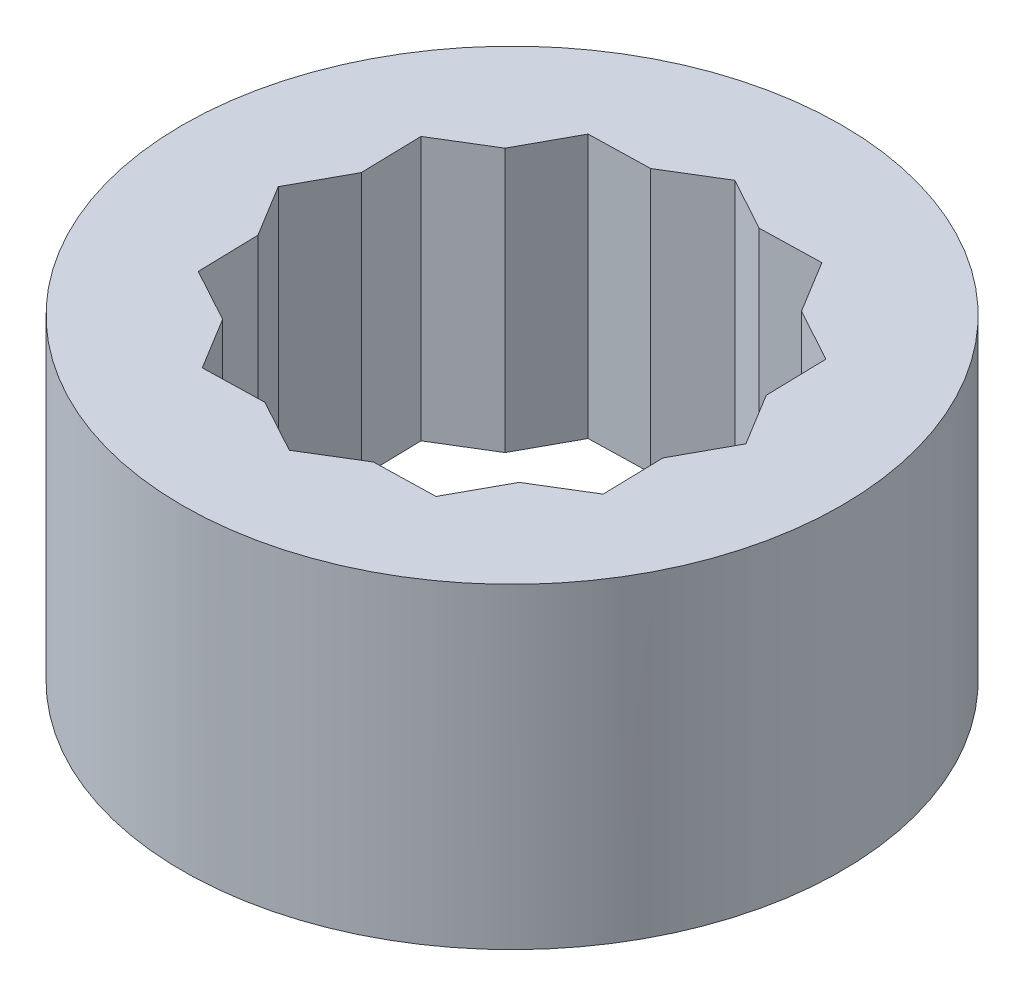
SolidWorks part; units mm, degrees
ref_plane "Front Plane" through (0, 0, 0) normal (0, 0, 1) x (1, 0, 0)
ref_plane "Top Plane" through (0, 0, 0) normal (0, 1, 0) x (1, 0, 0)
ref_plane "Right Plane" through (0, 0, 0) normal (1, 0, 0) x (0, 0, -1)
sketch "Sketch1" plane through (0, 0, 0) normal (0, 1, 0) x (1, 0, 0)
  circle A0 centre (0, 0) radius 15.875
  dimension "D1" = 31.75
extrude "Boss-Extrude1" add sketch "Sketch1" along normal blind 12.7 contours A0
sketch "Sketch2" plane through (0, 12.7, 0) normal (0, 1, 0) x (1, 0, 0)
  line L1 (9.6552, -5.2673) -> (9.3892, 5.728)
  line L2 (9.3892, 5.728) -> (-0.266, 10.9953)
  line L3 (-0.266, 10.9953) -> (-9.6552, 5.2673)
  line L4 (-9.6552, 5.2673) -> (-9.3892, -5.728)
  line L5 (-9.3892, -5.728) -> (0.266, -10.9953)
  line L6 (0.266, -10.9953) -> (9.6552, -5.2673)
  line L7 (5.728, -9.3892) -> (10.9953, 0.266)
  line L8 (10.9953, 0.266) -> (5.2673, 9.6552)
  line L9 (5.2673, 9.6552) -> (-5.728, 9.3892)
  line L10 (-5.728, 9.3892) -> (-10.9953, -0.266)
  line L11 (-10.9953, -0.266) -> (-5.2673, -9.6552)
  line L12 (-5.2673, -9.6552) -> (5.728, -9.3892)
  circle A0 centre (0, 0) radius 9.525 construction
  circle A1 centre (0, 0) radius 9.525 construction
  dimension "D1" = 19.05
extrude "Cut-Extrude1" cut sketch "Sketch2" against normal through all contours L5 L12 L6 L7 L1 L8 L2 L9 L3 L10 L4 L11 | L9 L10 L3 | L10 L3 L4 | L10 L11 L4 | L11 L4 L5 | L11 L12 L5 | L12 L5 L6 | L6 L12 L7 | L7 L6 L1 | L7 L8 L1 | L8 L1 L2 | L8 L9 L2 | L9 L2 L3
sketch "Sketch3" plane through (0, 0, 0) normal (0, -1, 0) x (1, 0, 0)
  circle A1 centre (0, 0) radius 15.875
  circle A2 centre (0, 0) radius 15.875
  dimension "D1" = 0
extrude "Boss-Extrude2" add sketch "Sketch3" along normal blind 2.54
sketch "Sketch4" plane through (0, -2.54, 0) normal (0, -1, 0) x (1, 0, 0)
  circle A2 centre (0, 0) radius 15.0813
  circle A3 centre (0, 0) radius 15.0813
  dimension "D1" = 0.7937
extrude "Cut-Extrude2" cut sketch "Sketch4" against normal blind 2.54
